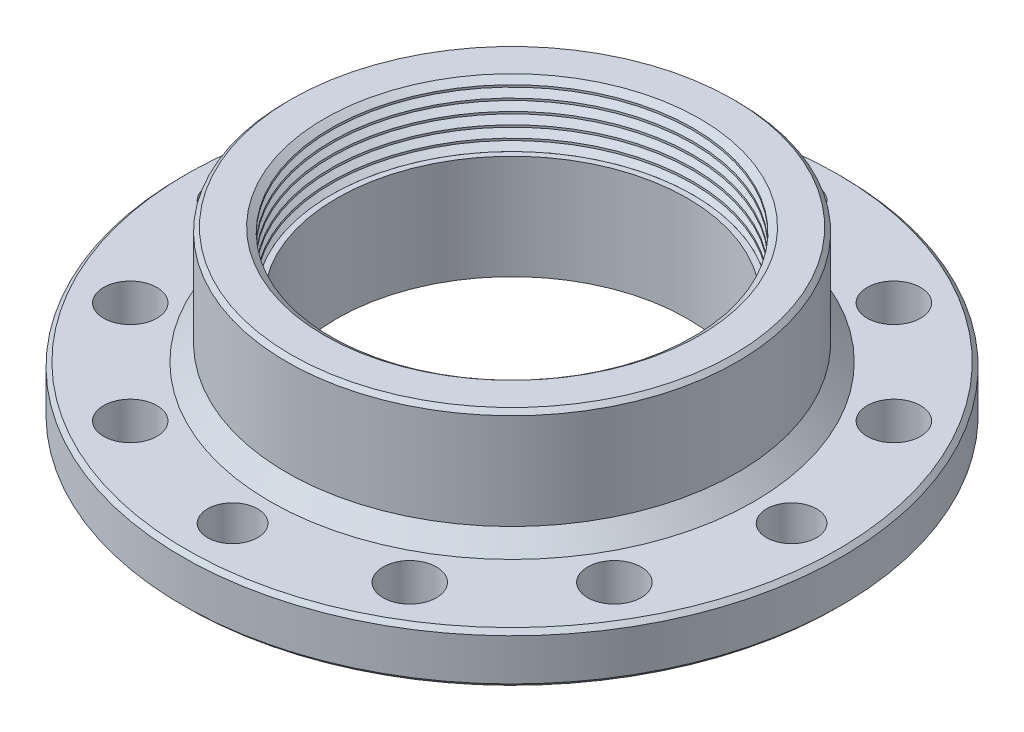
SolidWorks part; units mm, degrees
material " 09Г2С ГОСТ 4543-71"
ref_plane "Спереди" through (0, 0, 0) normal (0, 0, 1) x (1, 0, 0)
ref_plane "Сверху" through (0, 0, 0) normal (0, 1, 0) x (1, 0, 0)
ref_plane "Слева" through (0, 0, 0) normal (1, 0, 0) x (0, 0, -1)
sketch "Эскиз1" plane through (0, 0, 0) normal (0, 0, 1) x (1, 0, 0)
  line L0 (0, 0) -> (0, 25.1093) construction
  line L1 (-21, 0) -> (-41.109, 0)
  line L2 (-21, 0) -> (-21, 20)
  line L3 (-21, 20) -> (-27, 20)
  line L4 (-27, 6) -> (-27, 20)
  line L5 (-41.109, 0) -> (-39.5, 0)
  line L7 (-27, 6) -> (-39.5, 6)
  line L8 (-39.5, 0) -> (-39.5, 6)
  dimension "D1" = 20
  dimension "D2" = 6
  dimension "D3" = 12.5
  dimension "D4" = 42
revolve "Повернуть1" add sketch "Эскиз1" angle 360 about L0
chamfer "Фаска1" distance 2 angle 45 1 edges at (0, 6, -27)
chamfer "Фаска2" distance 0.5 angle 45 3 edges at (0, 0, -39.5) (0, 6, -39.5) (0, 20, -27)
sketch "Эскиз2" plane through (0, 6, 0) normal (0, 1, 0) x (1, 0, 0)
  line L1 (0, 33.5) -> (-16.75, 29.0119) construction
  line L2 (-16.75, 29.0119) -> (-29.0119, 16.75) construction
  line L3 (-29.0119, 16.75) -> (-33.5, 0) construction
  line L4 (-33.5, 0) -> (-29.0119, -16.75) construction
  line L5 (-29.0119, -16.75) -> (-16.75, -29.0119) construction
  line L6 (-16.75, -29.0119) -> (0, -33.5) construction
  line L7 (0, -33.5) -> (16.75, -29.0119) construction
  line L8 (16.75, -29.0119) -> (29.0119, -16.75) construction
  line L9 (29.0119, -16.75) -> (33.5, 0) construction
  line L10 (33.5, 0) -> (29.0119, 16.75) construction
  line L11 (29.0119, 16.75) -> (16.75, 29.0119) construction
  line L12 (16.75, 29.0119) -> (0, 33.5) construction
  circle A0 centre (0, 0) radius 33.5 construction
  circle A1 centre (0, 0) radius 39.5 construction
  circle A2 centre (-33.5, 0) radius 3
  circle A3 centre (0, 33.5) radius 3
  circle A4 centre (33.5, 0) radius 3
  circle A5 centre (0, -33.5) radius 3
  dimension "D1" = 6
  dimension "D2" = 6
hole_wizard "Отверстие с зазором M61" positions "Трехмерный эскиз1" profile "Эскиз3" hole size "M6" standard "ГОСТ" end condition through all
sketch3d "Трехмерный эскиз1"
  point P0 (-16.75, 6, 29.0119)
  point P3 (-29.0119, 6, -16.75)
  point P6 (16.75, 6, -29.0119)
  point P9 (29.0119, 6, 16.75)
  point P12 (-29.0119, 6, 16.75)
  point P15 (-16.75, 6, -29.0119)
  point P18 (29.0119, 6, -16.75)
  point P21 (16.75, 6, 29.0119)
sketch "Эскиз3" plane through (-16.75, 6, 29.0119) normal (1, 0, 0) x (0, 0, 1)
  line L0 (0, 0) -> (0, 6)
  line L1 (0, 6) -> (3.2, 6)
  line L2 (3.2, 6) -> (3.2, 0)
  line L5 (3.2, 0) -> (0, 0)
  line L11 (0, -6.35) -> (0, 107.95) construction
  dimension "Диаметр сквозного отверстия" = 6.4
  dimension "Глубина сквозного отверстия" = 6
extrude "Вытянуть1" cut sketch "Эскиз2" against normal through all
sketch "Эскиз6" plane through (0, 6, 0) normal (0, 1, 0) x (1, 0, 0)
  line L0 (0, -43.3983) -> (0, 0) construction
  line L1 (0, 0) -> (-31.5592, 31.5592) construction
  line L2 (-24.0416, 24.0416) -> (-23.3345, 23.3345)
  line L3 (-23.3345, 23.3345) -> (-23.3075, 23.343)
  arc A0 (-24.0416, 24.0416) -> (-23.3345, 23.3345) centre (-23.6881, 23.6881) ccw
  circle A1 centre (0, 0) radius 33.5 construction
  dimension "D2" = 0.5
  dimension "D1" = 135
revolve "Вырез-Повернуть2" cut sketch "Эскиз6" angle 360 about L1
sketch "Эскиз4" plane through (0, 20, 0) normal (0, 1, 0) x (1, 0, 0)
  circle A0 centre (0, 0) radius 21.688
  dimension "D1" = 43.376
extrude "Вытянуть2" cut sketch "Эскиз4" against normal blind 7.5
sketch "Эскиз5" plane through (0, 0, 0) normal (0, 0, 1) x (1, 0, 0)
  line L0 (-21.688, 20) -> (-26.5, 20) construction
  line L1 (-26.5, 20) -> (-27, 19.5) construction
  line L2 (-22.5, 20) -> (-21.688, 20.5686)
  line L3 (-21.688, 20.5686) -> (-15, 20.5686)
  line L4 (-15, 20.5686) -> (-15, 19.4314)
  line L5 (-21.688, 19.4314) -> (-15, 19.4314)
  line L6 (-22.5, 20) -> (-21.688, 19.4314)
  line L7 (-21.688, 20.5686) -> (-21.688, 19.4314) construction
  line L9 (0, 0) -> (0, 27.9638) construction
  point P10 (-15, 20)
  dimension "D1" = 70
  dimension "D2" = 30
  dimension "D3" = 45
  dimension "D4" = 1.1371
revolve "Вырез-Повернуть1" cut sketch "Эскиз5" angle 360 about L9
pattern_linear "Линейный массив1" count 6 spacing 1.386 along (0, -1, 0) of "Вырез-Повернуть1"
